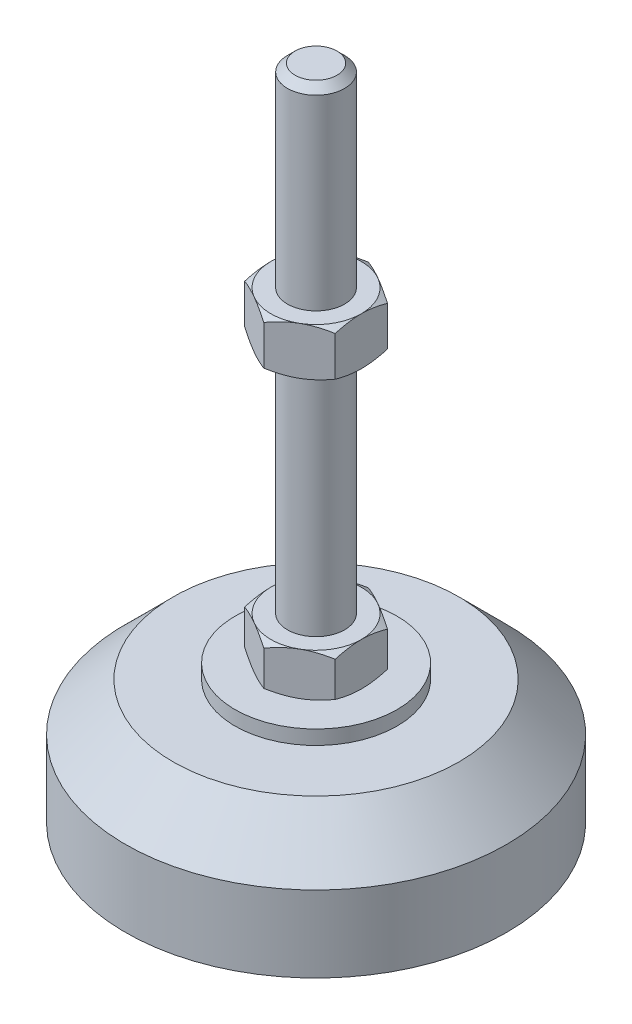
SolidWorks part; units mm, degrees
ref_plane "Спереди" through (0, 0, 0) normal (0, 0, 1) x (1, 0, 0)
ref_plane "Сверху" through (0, 0, 0) normal (0, 1, 0) x (1, 0, 0)
ref_plane "Справа" through (0, 0, 0) normal (1, 0, 0) x (0, 0, -1)
sketch "Эскиз1" plane through (0, 0, 0) normal (0, 0, 1) x (1, 0, 0)
  line L0 (0, 0) -> (-40, 0)
  line L3 (-40, 0) -> (-40, 16)
  line L5 (-17, 29) -> (-6, 29)
  line L12 (-6, 38) -> (-6, 136.4)
  line L13 (-6, 136.4) -> (-4.4, 138)
  line L14 (-4.4, 138) -> (0, 138)
  line L15 (0, 138) -> (0, 0) construction
  line L16 (-6, 29) -> (0, 29) construction
  line L17 (0, 0) -> (0, 138)
  line L18 (0, 0) -> (0, -7.9595) construction
  line L19 (-6, 38) -> (-6, 29)
  line L20 (-17, 29) -> (-17, 26)
  line L21 (-17, 26) -> (-30, 26)
  line L22 (-30, 26) -> (-40, 16)
  point P8 (-6, 87.2)
  point P23 (-11.5, 29)
  dimension "D1" = 12
  dimension "D2" = 29
  dimension "D3" = 9
  dimension "D4" = 80
  dimension "D5" = 6
  dimension "D6" = 1.6
  dimension "D7" = 45
  dimension "D8" = 34
  dimension "D10" = 100
  dimension "D11" = 16
  dimension "D12" = 45
  dimension "D13" = 3
revolve "Повернуть1" add sketch "Эскиз1" angle 360 about L17
sketch "Эскиз2" plane through (0, 29, 0) normal (0, 1, 0) x (1, 0, 0)
  line L1 (0, 10.9697) -> (-9.5, 5.4848)
  line L2 (-9.5, 5.4848) -> (-9.5, -5.4848)
  line L3 (-9.5, -5.4848) -> (0, -10.9697)
  line L4 (0, -10.9697) -> (9.5, -5.4848)
  line L5 (9.5, -5.4848) -> (9.5, 5.4848)
  line L6 (9.5, 5.4848) -> (0, 10.9697)
  circle A0 centre (0, 0) radius 9.5 construction
  dimension "D1" = 19
extrude "Бобышка-Вытянуть1" add sketch "Эскиз2" along normal up to vertex (9 mm away) up to point (-6, 38, 0)
ref_plane "Плоскость1" through (0, 87.2, 0) normal (0, 1, 0) x (1, 0, 0)
sketch "Эскиз3" plane through (0, 87.2, 0) normal (0, 1, 0) x (1, 0, 0)
  line L6 (9.5, 5.4848) -> (0, 10.9697)
  line L7 (0, 10.9697) -> (-9.5, 5.4848)
  line L8 (-9.5, 5.4848) -> (-9.5, -5.4848)
  line L9 (-9.5, -5.4848) -> (0, -10.9697)
  line L10 (0, -10.9697) -> (9.5, -5.4848)
  line L11 (9.5, -5.4848) -> (9.5, 5.4848)
  line L12 (9.5, 5.4848) -> (0, 10.9697)
  line L13 (0, 10.9697) -> (-9.5, 5.4848)
  line L14 (-9.5, 5.4848) -> (-9.5, -5.4848)
  line L15 (-9.5, -5.4848) -> (0, -10.9697)
  line L16 (0, -10.9697) -> (9.5, -5.4848)
  line L17 (9.5, -5.4848) -> (9.5, 5.4848)
  dimension "D1" = 0
extrude "Бобышка-Вытянуть2" add sketch "Эскиз3" along normal blind 10
sketch "Эскиз4" plane through (0, 0, 0) normal (0, 0, 1) x (1, 0, 0)
  line L0 (-9.5, 97.2) -> (-18.1603, 92.2)
  line L1 (-18.1603, 92.2) -> (-18.1603, 97.2)
  line L2 (-18.1603, 97.2) -> (-9.5, 97.2)
  line L3 (-18.1603, 92.2) -> (-9.5, 87.2)
  line L4 (50, 87.2) -> (-50, 87.2) construction
  line L5 (-9.5, 87.2) -> (-18.1603, 87.2)
  line L6 (-18.1603, 87.2) -> (-18.1603, 92.2)
  line L7 (-9.5, 97.2) -> (-9.5, 87.2) construction
  line L8 (-9.5, 38) -> (-17.2942, 38)
  line L9 (-17.2942, 38) -> (-17.2942, 33.5)
  line L10 (-17.2942, 33.5) -> (-9.5, 38)
  line L11 (-9.5, 29) -> (-17.2942, 33.5)
  line L12 (-17.2942, 33.5) -> (-17.2942, 29)
  line L13 (-17.2942, 29) -> (-9.5, 29)
  line L14 (0, 138) -> (0, 96.3793) construction
  dimension "D1" = 30
  dimension "D2" = 30
revolve "Вырез-Повернуть2" cut sketch "Эскиз4" angle 360 about L14
